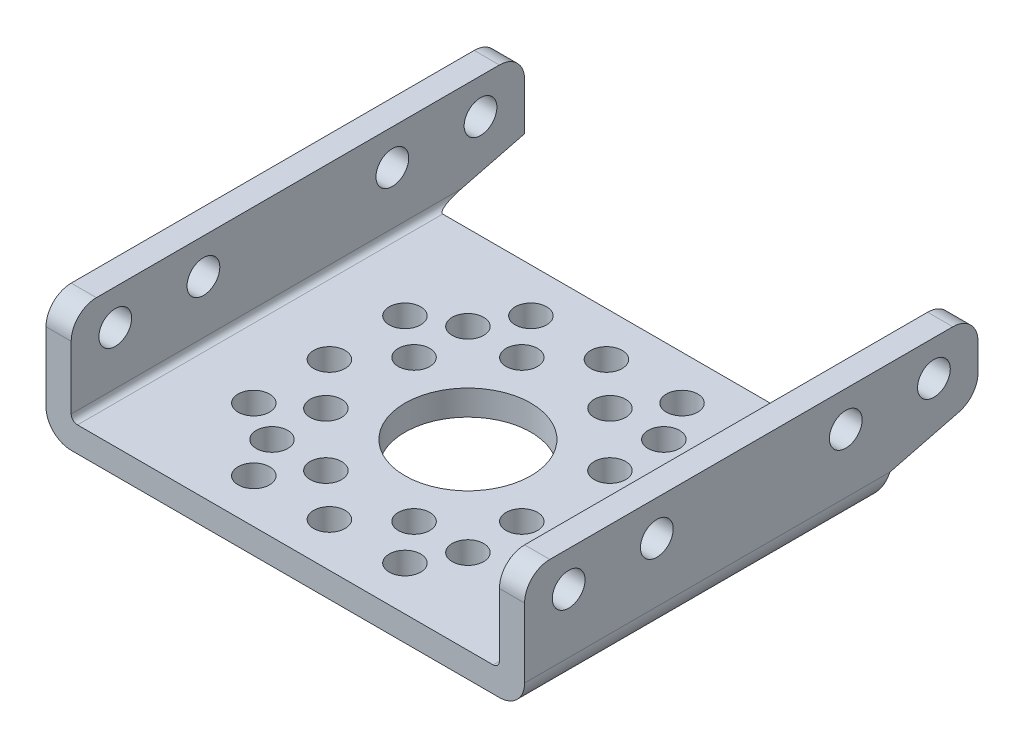
SolidWorks part; units mm, degrees
ref_plane "정면" through (0, 0, 0) normal (0, 0, 1) x (1, 0, 0)
ref_plane "윗면" through (0, 0, 0) normal (0, 1, 0) x (1, 0, 0)
ref_plane "우측면" through (0, 0, 0) normal (1, 0, 0) x (0, 0, -1)
sketch "스케치1" plane through (0, 0, 0) normal (0, 1, 0) x (1, 0, 0)
  line L1 (0, 0) -> (38, 0)
  line L2 (0, 0) -> (0, 29)
  line L3 (0, 29) -> (38, 29)
  line L4 (38, 0) -> (38, 29)
  dimension "D1" = 29
  dimension "D2" = 38
extrude "보스-돌출1" add sketch "스케치1" along normal blind 2
sketch "스케치2" plane through (0, 2, 0) normal (0, 1, 0) x (1, 0, 0)
  line L0 (0, 0) -> (38, 0) construction
  line L1 (2, 0) -> (0, 0)
  line L2 (2, 0) -> (2, 36)
  line L3 (2, 36) -> (0, 36)
  line L4 (0, 0) -> (0, 36)
  line L5 (19, 34.8406) -> (19, -6.4326) construction
  line L10 (36, 36) -> (38, 36)
  line L11 (38, 0) -> (38, 36)
  line L12 (36, 0) -> (38, 0)
  line L13 (36, 0) -> (36, 36)
  dimension "D1" = 2
  dimension "D2" = 36
extrude "보스-돌출2" add sketch "스케치2" along normal blind 7.5
sketch "스케치3" plane through (0, 2, 0) normal (0, 1, 0) x (1, 0, 0)
  line L0 (19, 40.11) -> (19, -9.6576) construction
  circle A0 centre (19, 14.5) radius 5
  circle A1 centre (19, 25.5) radius 1.25
  circle A2 centre (26.7782, 22.2782) radius 1.25
  circle A3 centre (30, 14.5) radius 1.25
  circle A4 centre (26.7782, 6.7218) radius 1.25
  circle A5 centre (19, 3.5) radius 1.25
  circle A6 centre (11.2218, 6.7218) radius 1.25
  circle A7 centre (8, 14.5) radius 1.25
  circle A8 centre (11.2218, 22.2782) radius 1.25
  circle A9 centre (13, 25.5) radius 1.25
  circle A10 centre (25, 25.5) radius 1.25
  circle A11 centre (30, 20.5) radius 1.25
  circle A12 centre (30, 8.5) radius 1.25
  circle A13 centre (25, 3.5) radius 1.25
  circle A14 centre (13, 3.5) radius 1.25
  circle A15 centre (8, 8.5) radius 1.25
  circle A16 centre (8, 20.5) radius 1.25
  circle A17 centre (15.5, 22.2782) radius 1.25
  circle A18 centre (22.5, 22.2782) radius 1.25
  circle A19 centre (26.7782, 18) radius 1.25
  circle A20 centre (26.7782, 11) radius 1.25
  circle A21 centre (22.5, 6.7218) radius 1.25
  circle A22 centre (15.5, 6.7218) radius 1.25
  circle A23 centre (11.2218, 11) radius 1.25
  circle A24 centre (11.2218, 18) radius 1.25
  point P20 (19, 14.5)
  point P40 (19, 14.5)
  point P57 (19, 14.5)
  dimension "D1" = 10
  dimension "D2" = 2.5
  dimension "D5" = 2.5
  dimension "D8" = 2.5
  dimension "D3" = 11
  dimension "D6" = 6
  dimension "D9" = 3.5
  dimension "D4" = 8
  dimension "D7" = 4
  dimension "D10" = 4
extrude "컷-돌출1" cut sketch "스케치3" against normal through all both and the other way through all
sketch "스케치4" plane through (38, 0, 0) normal (1, 0, 0) x (0, 0, -1)
  line L0 (0, 0) -> (29, 0) construction
  circle A0 centre (3.5, 6.7) radius 1.3
  circle A1 centre (25.5, 6.7) radius 1.3
  circle A2 centre (10.5, 6.7) radius 1.3
  circle A3 centre (32.5, 6.7) radius 1.3
  point P10 (14.5, 0)
  dimension "D1" = 2.6
  dimension "D2" = 6.7
  dimension "D3" = 2.6
  dimension "D4" = 22
  dimension "D5" = 2.6
  dimension "D6" = 2.6
  dimension "D7" = 22
  dimension "D8" = 7
  dimension "D9" = 4
extrude "컷-돌출2" cut sketch "스케치4" against normal through all
sketch "스케치5" plane through (38, 0, 0) normal (1, 0, 0) x (0, 0, -1)
  line L0 (29, 2) -> (28.1163, 0)
  line L1 (0, 0) -> (29, 0) construction
  line L2 (28.1163, 0) -> (29, 0)
  line L3 (29, 0) -> (29, 2)
  line L4 (29, 2) -> (36, 3.7709)
  line L5 (36, 9.5) -> (36, 2) construction
  line L6 (36, 3.7709) -> (36, 2)
  line L7 (36, 2) -> (29, 2)
  line M7 (29, 2) -> (36, 2)
  line M8 (36, 2) -> (36, 9.5)
extrude "컷-돌출3" cut sketch "스케치5" against normal through all contours L4 M7 M8 | L0 L2 L3
fillet "필렛1" radius 2 5 edges at (37, 3.7709, -36) (1, 9.5, -36) (37, 9.5, -36) (1, 9.5, 0) (37, 9.5, 0)
fillet "필렛3" radius 0.5 2 edges at (36, 2, -14.5) (2, 2, -14.5)
fillet "필렛4" radius 2 2 edges at (0, 0, -14.0582) (38, 0, -14.0582)
